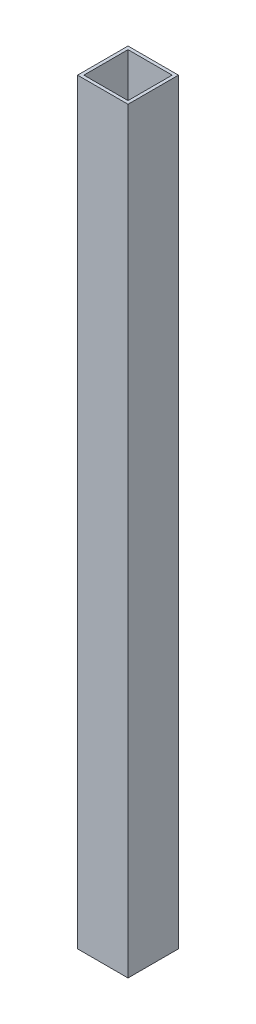
SolidWorks part; units mm, degrees
ref_plane "Front Plane" through (0, 0, 0) normal (0, 0, 1) x (1, 0, 0)
ref_plane "Top Plane" through (0, 0, 0) normal (0, 1, 0) x (1, 0, 0)
ref_plane "Right Plane" through (0, 0, 0) normal (1, 0, 0) x (0, 0, -1)
sketch "Sketch1" plane through (0, 0, 0) normal (0, 1, 0) x (1, 0, 0)
  line L0 (-11.1125, 11.1125) -> (-11.1125, -11.1125)
  line L1 (12.7, 12.7) -> (-12.7, 12.7)
  line L2 (12.7, 12.7) -> (12.7, -12.7)
  line L3 (12.7, -12.7) -> (-12.7, -12.7)
  line L4 (-12.7, 12.7) -> (-12.7, -12.7)
  line L5 (12.7, 12.7) -> (-12.7, -12.7) construction
  line L6 (12.7, -12.7) -> (-12.7, 12.7) construction
  line L7 (11.1125, -11.1125) -> (-11.1125, -11.1125)
  line L8 (11.1125, 11.1125) -> (11.1125, -11.1125)
  line L9 (11.1125, 11.1125) -> (-11.1125, 11.1125)
  point P0 (0, 0)
  dimension "D1" = 25.4
  dimension "D2" = 1.5875
extrude "Boss-Extrude1" add sketch "Sketch1" along normal blind 381
